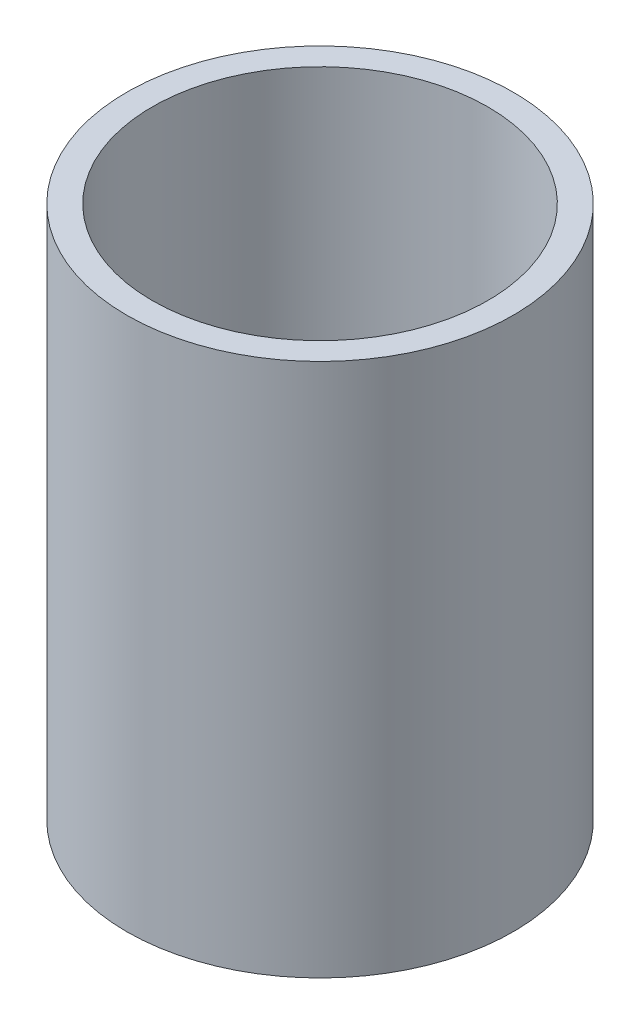
SolidWorks part; units mm, degrees
material "Corrugated Paper"
ref_plane "Front Plane" through (0, 0, 0) normal (0, 0, 1) x (1, 0, 0)
ref_plane "Top Plane" through (0, 0, 0) normal (0, 1, 0) x (1, 0, 0)
ref_plane "Right Plane" through (0, 0, 0) normal (1, 0, 0) x (0, 0, -1)
ref_axis "Axis1" through (0, 55, 0) along (0, -1, 0)
sketch "Sketch1" plane through (0, 0, 0) normal (0, 0, 1) x (1, 0, 0)
  line L1 (-48.26, 45.6176) -> (-41.91, 45.6176)
  line L2 (-48.26, 45.6176) -> (-48.26, -87.7324)
  line L3 (-48.26, -87.7324) -> (-41.91, -87.7324)
  line L4 (-41.91, 45.6176) -> (-41.91, -87.7324)
  line L5 (-38.1, 45.6176) -> (0, 45.6176) construction
  line L6 (-38.1, -87.7324) -> (0, -87.7324) construction
revolve "Revolve1" add sketch "Sketch1" angle 360 about axis through (0, 55, 0) along (0, -1, 0)
